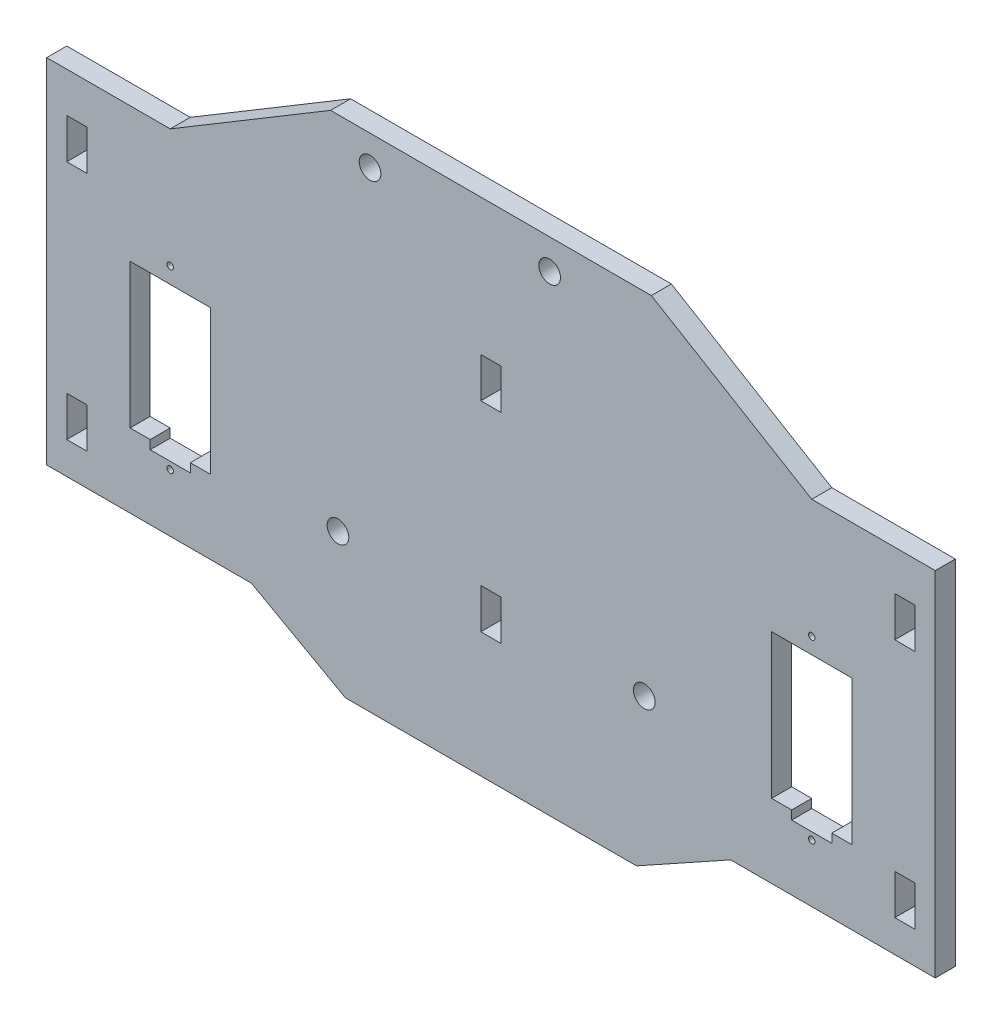
SolidWorks part; units mm, degrees
ref_plane "Front Plane" through (0, 0, 0) normal (0, 0, 1) x (1, 0, 0)
ref_plane "Top Plane" through (0, 0, 0) normal (0, 1, 0) x (1, 0, 0)
ref_plane "Right Plane" through (0, 0, 0) normal (1, 0, 0) x (0, 0, -1)
sketch "Sketch1" plane through (0, 0, 0) normal (0, 0, 1) x (1, 0, 0)
  line L1 (-70.358, -27.94) -> (70.358, -27.94)
  line L2 (-70.358, -27.94) -> (-70.358, 27.94)
  line L3 (-70.358, 27.94) -> (70.358, 27.94)
  line L4 (70.358, -27.94) -> (70.358, 27.94)
  line L5 (-70.358, -27.94) -> (70.358, 27.94) construction
  line L6 (-70.358, 27.94) -> (70.358, -27.94) construction
  point P0 (0, 0)
  dimension "D1" = 140.716
  dimension "D2" = 55.88
extrude "Boss-Extrude1" add sketch "Sketch1" along normal blind 3.175
sketch "Sketch2" plane through (0, 0, 3.175) normal (0, 0, 1) x (1, 0, 0)
  line L0 (70.358, 27.94) -> (-70.358, 27.94) construction
  line L1 (-67.183, 21.59) -> (-63.9572, 21.59)
  line L2 (-67.183, 21.59) -> (-67.183, 15.24)
  line L3 (-67.183, 15.24) -> (-63.9572, 15.24)
  line L4 (-63.9572, 21.59) -> (-63.9572, 15.24)
  line L5 (-67.183, 21.59) -> (-63.9572, 15.24) construction
  line L6 (-67.183, 15.24) -> (-63.9572, 21.59) construction
  line L7 (-67.183, -16.51) -> (-63.9572, -16.51)
  line L8 (-67.183, -16.51) -> (-67.183, -22.86)
  line L9 (-67.183, -22.86) -> (-63.9572, -22.86)
  line L10 (-63.9572, -16.51) -> (-63.9572, -22.86)
  line L11 (-67.183, -16.51) -> (-63.9572, -22.86) construction
  line L12 (-67.183, -22.86) -> (-63.9572, -16.51) construction
  line L14 (-70.358, 27.94) -> (-70.358, -27.94) construction
  point P0 (-65.5701, 18.415)
  point P5 (-65.5701, -19.685)
  dimension "D1" = 6.35
  dimension "D2" = 6.35
  dimension "D3" = 3.2258
  dimension "D4" = 3.2258
  dimension "D5" = 6.35
  dimension "D6" = 31.75
  dimension "D7" = 3.175
  dimension "D8" = 3.175
extrude "holes for tabs" cut sketch "Sketch2" against normal through all
mirror "Mirror1" about plane through (0, 0, 0) normal (1, 0, 0) of "holes for tabs"
sketch "Sketch3" plane through (0, 0, 3.175) normal (0, 0, 1) x (1, 0, 0)
  line L1 (-1.6129, 21.5905) -> (1.6129, 21.5905)
  line L2 (-1.6129, 21.5905) -> (-1.6129, 15.2405)
  line L3 (-1.6129, 15.2405) -> (1.6129, 15.2405)
  line L4 (1.6129, 21.5905) -> (1.6129, 15.2405)
  line L5 (-1.6129, 21.5905) -> (1.6129, 15.2405) construction
  line L6 (-1.6129, 15.2405) -> (1.6129, 21.5905) construction
  line L7 (-1.6129, -10.0891) -> (1.6129, -10.0891)
  line L8 (-1.6129, -10.0891) -> (-1.6129, -16.4391)
  line L9 (-1.6129, -16.4391) -> (1.6129, -16.4391)
  line L10 (1.6129, -10.0891) -> (1.6129, -16.4391)
  line L11 (-1.6129, -10.0891) -> (1.6129, -16.4391) construction
  line L12 (-1.6129, -16.4391) -> (1.6129, -10.0891) construction
  line L13 (70.358, 27.94) -> (-70.358, 27.94) construction
  line L14 (0, 27.94) -> (0, -27.94) construction
  line L15 (70.358, 27.94) -> (-70.358, 27.94) construction
  line L16 (-70.358, -27.94) -> (70.358, -27.94) construction
  point P0 (0, 18.4155)
  point P5 (0, -13.2641)
  dimension "D1" = 6.35
  dimension "D2" = 6.35
  dimension "D3" = 3.2258
  dimension "D4" = 3.2258
  dimension "D5" = 6.3495
  dimension "D6" = 38.0291
extrude "cut for tabs, nosepanel" cut sketch "Sketch3" against normal through all
sketch "Sketch5" plane through (0, 0, 3.175) normal (0, 0, 1) x (1, 0, 0)
  line L0 (0, 0) -> (0, 10.6338) construction
  line B0 (-44.45, 6.604) -> (-57.15, 6.604)
  line B1 (-44.45, 6.604) -> (-44.45, -16.256)
  line B2 (-44.45, -16.256) -> (-47.625, -16.256)
  line B3 (-57.15, 6.604) -> (-57.15, -16.256)
  line B4 (-47.625, -16.256) -> (-47.625, -17.653)
  line B5 (-47.625, -17.653) -> (-53.975, -17.653)
  line B6 (-53.975, -16.256) -> (-53.975, -17.653)
  line B7 (-53.975, -16.256) -> (-57.15, -16.256)
  circle B8 centre (-50.8, -18.796) radius 0.508
  circle B9 centre (-50.8, 9.144) radius 0.508
  dimension "D1" = 50.8
  dimension "D2" = 10.16
sketch_block_instance "servo_hole_SG90-1"
sketch_block "servo_hole_SG90" parameters "D5"=1.016, "D6"=1.016, "D9"=2.1092, "D1"=27.94, "D2"=6.35, "D3"=22.86, "D4"=12.7, "D7"=1.397, "D8"=6.35
extrude "cut for optional motors (ears)" cut sketch "Sketch5" against normal through all
mirror "Mirror2" about plane through (0, 0, 0) normal (1, 0, 0) of "cut for optional motors (ears)"
sketch "Sketch6" plane through (0, 0, 3.175) normal (0, 0, 1) x (1, 0, 0)
  line L0 (0, 0) -> (0, -48.2618) construction
  line L1 (0, -27.94) -> (0, -36.2186)
  line L3 (-70.358, -27.94) -> (70.358, -27.94) construction
  line L4 (0, -36.2186) -> (-23.0519, -36.2186)
  line L5 (-23.0519, -36.2186) -> (-37.9538, -27.94)
  line L6 (0, 27.94) -> (0, 43.18)
  line L7 (70.358, 27.94) -> (-70.358, 27.94) construction
  line L8 (0, 43.18) -> (-25.4, 43.18)
  line L9 (-25.4, 43.18) -> (-50.8, 27.94)
  line L10 (-50.8, 27.94) -> (0, 27.94)
  line L11 (-37.9538, -27.94) -> (0, -27.94)
  dimension "D3" = 50.8
  dimension "D4" = 25.4
  dimension "D5" = 15.24
extrude "Boss-Extrude2" add sketch "Sketch6" against normal blind 3.175
mirror "Mirror3" about plane through (0, 0, 0) normal (1, 0, 0) of "Boss-Extrude2"
sketch "Sketch7" plane through (0, 0, 0) normal (0, 0, -1) x (-1, 0, 0)
  line L1 (-25.4, 43.18) -> (25.4, 43.18) construction
  line B0 (-9.2934, 38.4302) -> (19.1546, 38.4302) construction
  line B1 (-26.8194, 40.64) -> (26.7746, 40.64) construction
  line B2 (26.7746, 40.64) -> (26.7746, -27.9908) construction
  line B3 (26.7746, -27.9908) -> (-26.8194, -27.9908) construction
  line B4 (-26.8194, -27.9908) -> (-26.8194, 40.64) construction
  circle B5 centre (19.1546, 38.4302) radius 1.7145
  circle B6 centre (-9.2934, 38.4302) radius 1.7145
  circle B7 centre (24.2346, -13.97) radius 1.7145
  circle B8 centre (-24.2794, -12.319) radius 1.7145
  dimension "D1" = 2.54
sketch_block_instance "Block2-1"
sketch_block "Block2" parameters "D1"=3.429, "D2"=3.429, "D3"=3.429, "D4"=3.429, "D5"=14.0208, "D6"=51.054, "D7"=15.6718, "D8"=66.421, "D9"=7.62, "D10"=36.068
extrude "cut for arduino mount holes" cut sketch "Sketch7" against normal through all
